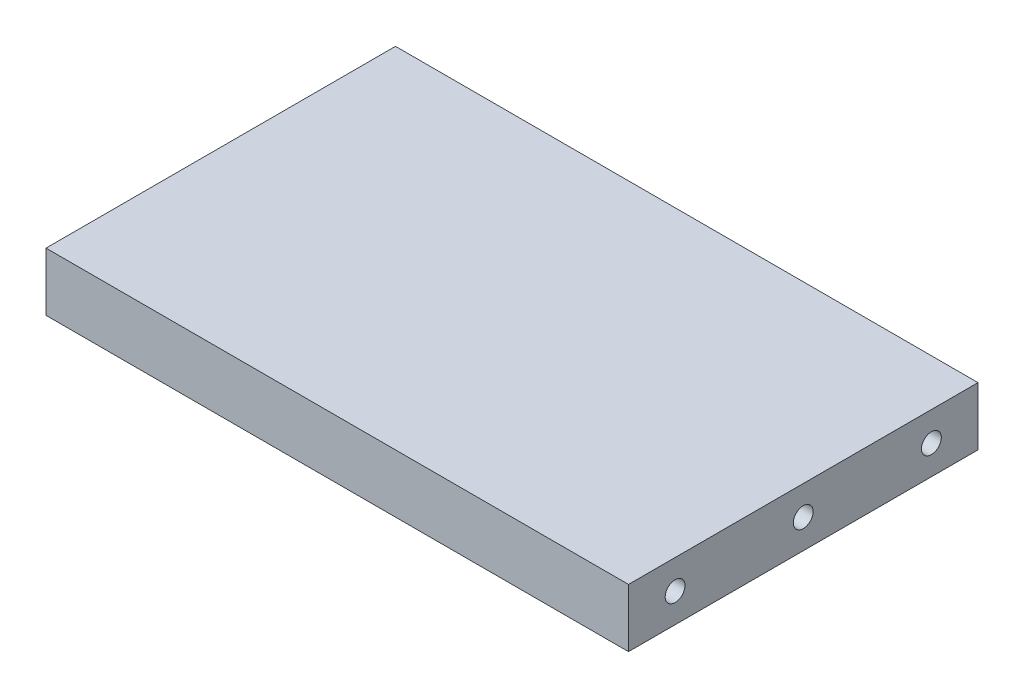
SolidWorks part; units mm, degrees
material "Plain Carbon Steel"
ref_plane "Front Plane" through (0, 0, 0) normal (0, 0, 1) x (1, 0, 0)
ref_plane "Top Plane" through (0, 0, 0) normal (0, 1, 0) x (1, 0, 0)
ref_plane "Right Plane" through (0, 0, 0) normal (1, 0, 0) x (0, 0, -1)
sketch "Sketch1" plane through (0, 0, 0) normal (0, 1, 0) x (1, 0, 0)
  line L1 (-50, -30) -> (50, -30)
  line L2 (-50, -30) -> (-50, 30)
  line L3 (-50, 30) -> (50, 30)
  line L4 (50, -30) -> (50, 30)
  line L5 (-50, -30) -> (50, 30) construction
  line L6 (-50, 30) -> (50, -30) construction
  point P0 (0, 0)
  dimension "D1" = 100
  dimension "D2" = 60
extrude "Boss-Extrude1" add sketch "Sketch1" along normal blind 10
hole_wizard "CBORE for M3 SHCS1" positions "Sketch2" profile "Sketch3" counterbore size "M3" standard "ANSI Metric"
sketch "Sketch2" plane through (60, -888.0121, -1303.2827) normal (1, 0, 0) x (0, 0, -1)
  line L0 (-1281.2827, 893.0121) -> (-1325.2827, 893.0121) construction
  point P0 (-1281.2827, 893.0121)
  point P1 (-1325.2827, 893.0121)
  point P9 (-1303.2827, 893.0121)
sketch "Sketch3" plane through (60, 5, -22) normal (0, 1, 0) x (0, 0, -1)
  line L0 (0, 0) -> (0, 24.0215)
  line L1 (0, 24.0215) -> (1.7, 23)
  line L2 (1.7, 23) -> (1.7, 3)
  line L3 (1.7, 3) -> (3.25, 3)
  line L4 (3.25, 3) -> (3.25, 0)
  line L5 (3.25, 0) -> (0, 0)
  line L6 (0, 24.0215) -> (-1.7, 23) construction
  line L7 (0, -6.35) -> (0, 107.95) construction
  dimension "Hole Dia." = 3.4
  dimension "Hole Depth" = 23
  dimension "C'Bore Dia." = 6.5
  dimension "C'Bore Depth" = 3
  dimension "Drill Angle" = 118
hole_wizard "CBORE for M3 SHCS2" positions "Sketch4" profile "Sketch5" counterbore size "M3" standard "ANSI Metric"
sketch "Sketch4" plane through (-60, -888.0121, -1303.2827) normal (-1, 0, 0) x (0, 0, 1)
  line L0 (1281.2827, 893.0121) -> (1325.2827, 893.0121) construction
  point P0 (1281.2827, 893.0121)
  point P1 (1325.2827, 893.0121)
  point P4 (1303.2827, 893.0121)
sketch "Sketch5" plane through (-60, 5, -22) normal (0, 1, 0) x (0, 0, 1)
  line L0 (0, 0) -> (0, 24.0215)
  line L1 (0, 24.0215) -> (1.7, 23)
  line L2 (1.7, 23) -> (1.7, 3)
  line L3 (1.7, 3) -> (3.25, 3)
  line L4 (3.25, 3) -> (3.25, 0)
  line L5 (3.25, 0) -> (0, 0)
  line L6 (0, 24.0215) -> (-1.7, 23) construction
  line L7 (0, -6.35) -> (0, 107.95) construction
  dimension "Hole Dia." = 3.4
  dimension "Hole Depth" = 23
  dimension "C'Bore Dia." = 6.5
  dimension "C'Bore Depth" = 3
  dimension "Drill Angle" = 118
